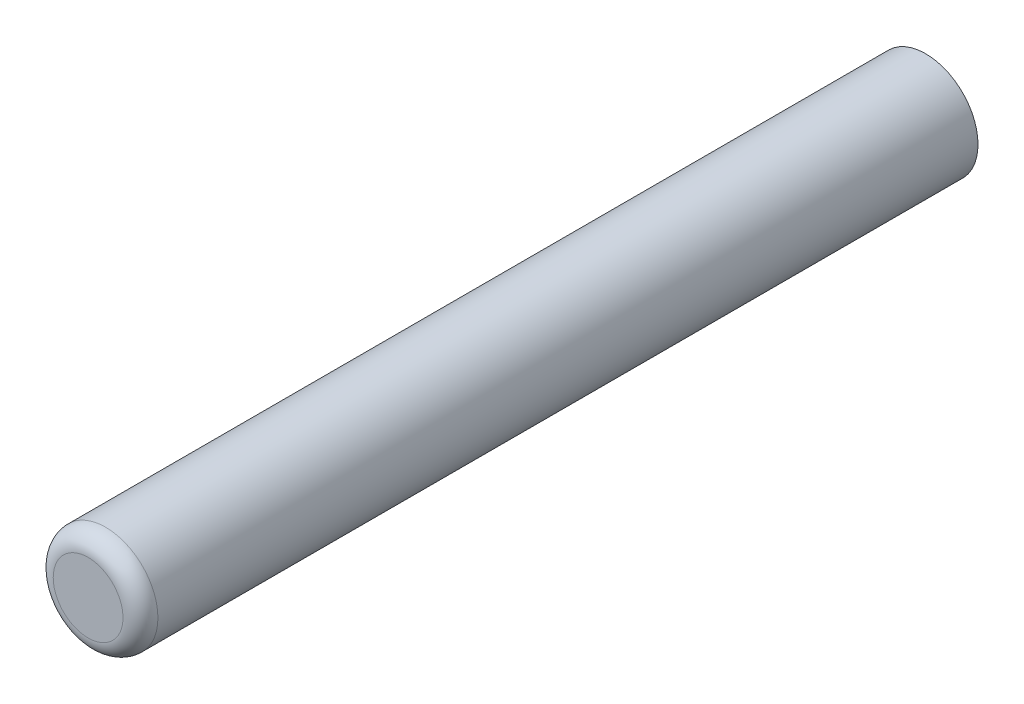
SolidWorks part; units mm, degrees
material "AISI 1020 Steel, Cold Rolled"
ref_plane "Front" through (0, 0, 0) normal (0, 0, 1) x (1, 0, 0)
ref_plane "Top" through (0, 0, 0) normal (0, 1, 0) x (1, 0, 0)
ref_plane "Right" through (0, 0, 0) normal (1, 0, 0) x (0, 0, -1)
sketch "Sketch2" plane through (0, 0, 0) normal (1, 0, 0) x (0, 0, -1)
  line L0 (0, 0) -> (93.1591, 0) construction
  line L1 (0, 0) -> (0, 4.7625)
  line L2 (0, 4.7625) -> (76.2, 4.7625)
  line L3 (76.2, 4.7625) -> (76.2, 0)
  line L4 (76.2, 0) -> (0, 0)
  dimension "D1" = 76.2
  dimension "D2" = 9.525
revolve "Revolve1" add sketch "Sketch2" angle 360 about L0
fillet "Fillet1" radius 1.5875 1 edges at (4.7625, 0, 0)
